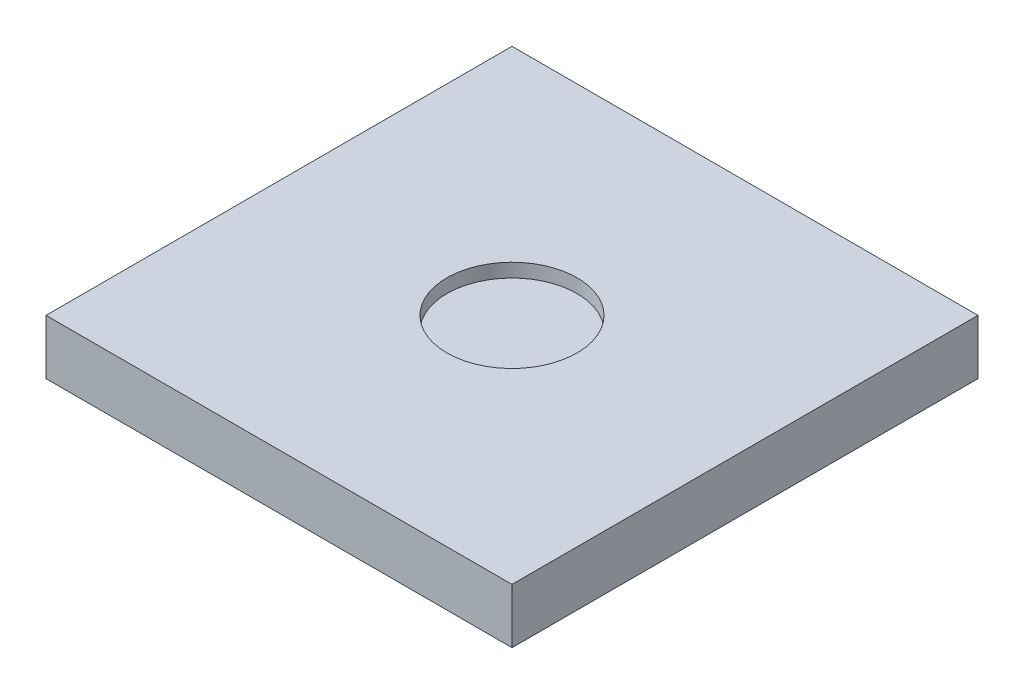
SolidWorks part; units mm, degrees
ref_plane "Front Plane" through (0, 0, 0) normal (0, 0, 1) x (1, 0, 0)
ref_plane "Top Plane" through (0, 0, 0) normal (0, 1, 0) x (1, 0, 0)
ref_plane "Right Plane" through (0, 0, 0) normal (1, 0, 0) x (0, 0, -1)
sketch "Sketch1" plane through (0, 0, 0) normal (0, 1, 0) x (1, 0, 0)
  line L1 (170, 170) -> (-170, 170)
  line L2 (170, 170) -> (170, -170)
  line L3 (170, -170) -> (-170, -170)
  line L4 (-170, 170) -> (-170, -170)
  line L5 (170, 170) -> (-170, -170) construction
  line L6 (170, -170) -> (-170, 170) construction
  point P0 (0, 0)
  dimension "D1" = 340
  dimension "D2" = 340
extrude "Boss-Extrude1" add sketch "Sketch1" along normal blind 40
sketch "Sketch2" plane through (0, 40, 0) normal (0, 1, 0) x (1, 0, 0)
  circle A0 centre (0, 0) radius 47.5
  dimension "D1" = 95
extrude "Cut-Extrude1" cut sketch "Sketch2" against normal blind 10 contours A0
